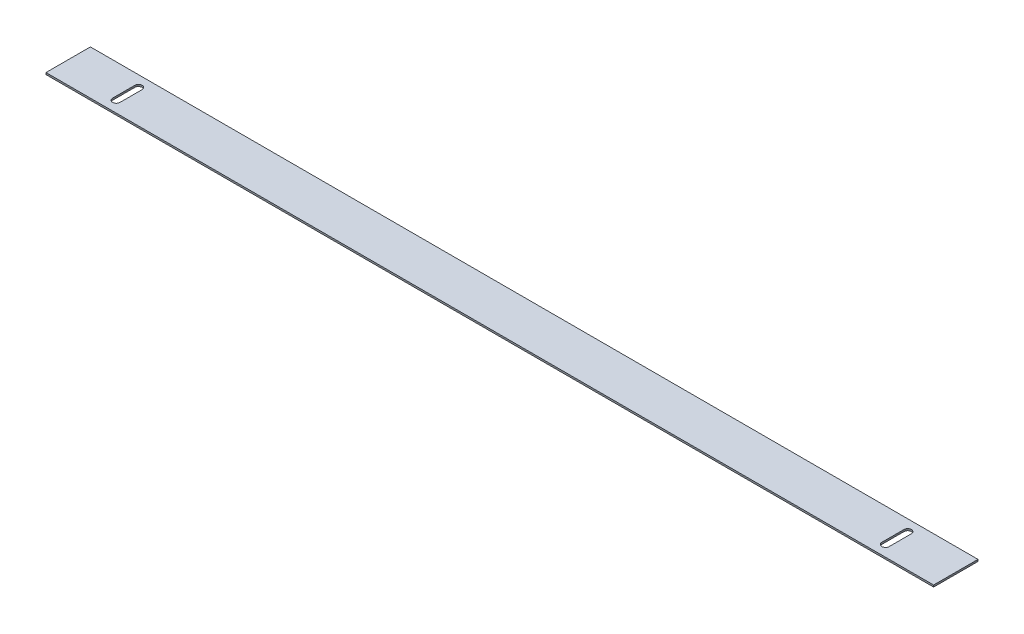
SolidWorks part; units mm, degrees
material "Mahogany"
ref_plane "Front Plane" through (0, 0, 0) normal (0, 0, 1) x (1, 0, 0)
ref_plane "Top Plane" through (0, 0, 0) normal (0, 1, 0) x (1, 0, 0)
ref_plane "Right Plane" through (0, 0, 0) normal (1, 0, 0) x (0, 0, -1)
sketch "Sketch1" plane through (0, 0, 0) normal (0, 1, 0) x (1, 0, 0)
  line L0 (-330.2, 9.525) -> (-330.2, -9.525) construction
  line L1 (-381, 19.05) -> (381, 19.05)
  line L2 (-381, 19.05) -> (-381, -19.05)
  line L3 (-381, -19.05) -> (381, -19.05)
  line L4 (381, 19.05) -> (381, -19.05)
  line L5 (-327.025, 9.525) -> (-327.025, -9.525)
  line L6 (-333.375, 9.525) -> (-333.375, -9.525)
  line L7 (0, 60.1695) -> (0, -81.5572) construction
  line L8 (330.2, 9.525) -> (330.2, -9.525) construction
  line L9 (327.025, 9.525) -> (327.025, -9.525)
  line L10 (333.375, 9.525) -> (333.375, -9.525)
  arc A0 (-327.025, 9.525) -> (-333.375, 9.525) centre (-330.2, 9.525) ccw
  arc A1 (-333.375, -9.525) -> (-327.025, -9.525) centre (-330.2, -9.525) ccw
  arc A2 (327.025, 9.525) -> (333.375, 9.525) centre (330.2, 9.525) cw
  arc A3 (333.375, -9.525) -> (327.025, -9.525) centre (330.2, -9.525) cw
  point P7 (-330.2, 0)
  point P16 (330.2, 0)
  dimension "D1" = 762
  dimension "D2" = 38.1
  dimension "D3" = 381
  dimension "D4" = 19.05
  dimension "D5" = 19.05
  dimension "D6" = 6.35
  dimension "D7" = 19.05
  dimension "D8" = 50.8
extrude "Boss-Extrude1" add sketch "Sketch1" along normal mid plane 1.5875
split "Split1" trim tools "Top Plane" bodies to split 101 resulting bodies 102 103
